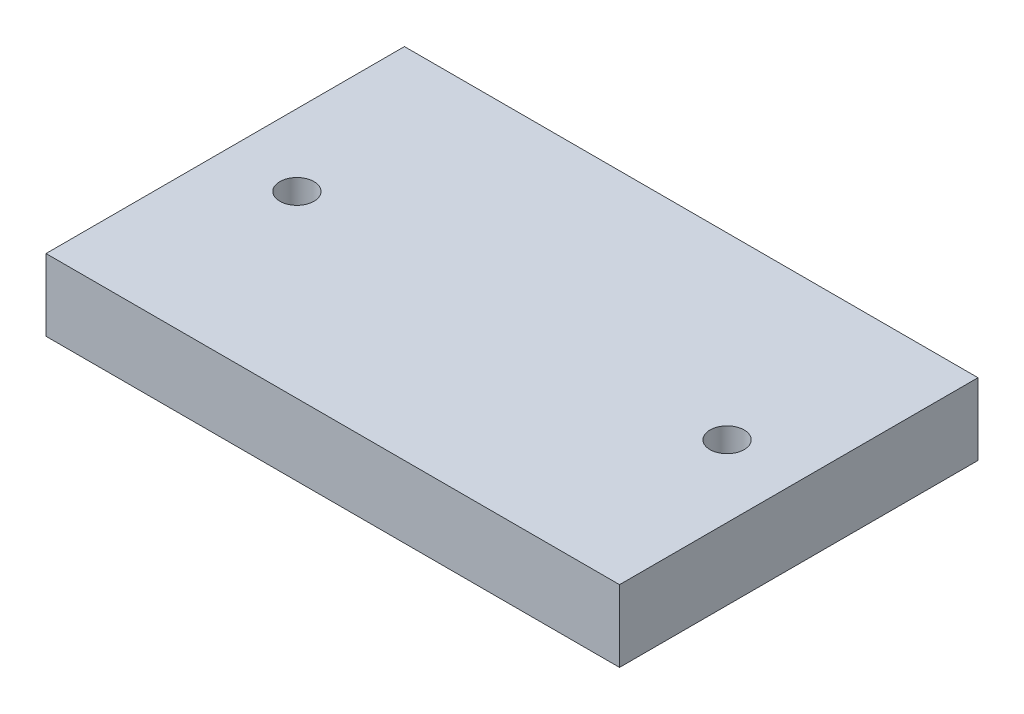
SolidWorks part; units mm, degrees
ref_plane "Front Plane" through (0, 0, 0) normal (0, 0, 1) x (1, 0, 0)
ref_plane "Top Plane" through (0, 0, 0) normal (0, 1, 0) x (1, 0, 0)
ref_plane "Right Plane" through (0, 0, 0) normal (1, 0, 0) x (0, 0, -1)
sketch "Sketch1" plane through (0, 0, 0) normal (0, 1, 0) x (1, 0, 0)
  line L1 (-40, -25) -> (40, -25)
  line L2 (-40, -25) -> (-40, 25)
  line L3 (-40, 25) -> (40, 25)
  line L4 (40, -25) -> (40, 25)
  line L5 (-40, -25) -> (40, 25) construction
  line L6 (-40, 25) -> (40, -25) construction
  point P0 (0, 0)
  dimension "D1" = 80
  dimension "D2" = 50
extrude "Boss-Extrude1" add sketch "Sketch1" along normal blind 10
sketch "Sketch2" plane through (0, 10, 0) normal (0, 1, 0) x (1, 0, 0)
  line L0 (-40, 25) -> (-40, -25) construction
  line L1 (40, -25) -> (40, 25) construction
  circle A0 centre (-30, 0) radius 2.3813
  circle A1 centre (30, 0) radius 2.3812
  dimension "D1" = 4.7625
  dimension "D2" = 4.7625
  dimension "D3" = 10
  dimension "D4" = 10
extrude "Cut-Extrude1" cut sketch "Sketch2" against normal blind 10
